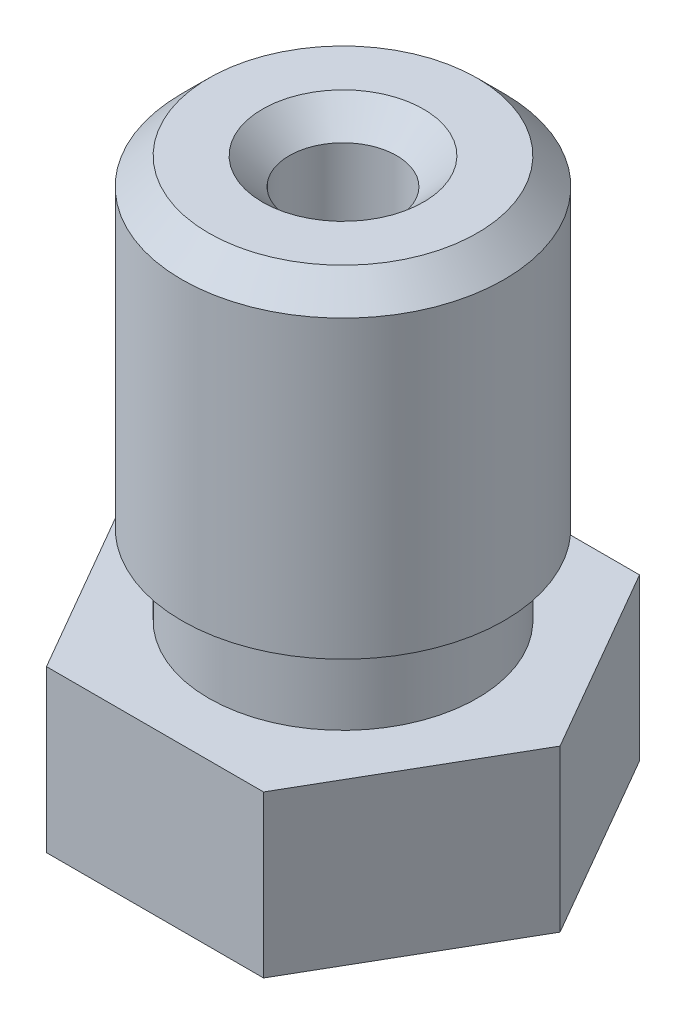
SolidWorks part; units mm, degrees
material "Brass"
ref_plane "Front Plane" through (0, 0, 0) normal (0, 0, 1) x (1, 0, 0)
ref_plane "Top Plane" through (0, 0, 0) normal (0, 1, 0) x (1, 0, 0)
ref_plane "Right Plane" through (0, 0, 0) normal (1, 0, 0) x (0, 0, -1)
ref_plane "Plane1" through (0, 0, 0) normal (0, -1, 0) x (1, 0, 0)
sketch "Sketch1" plane through (0, 0, 0) normal (0, -1, 0) x (1, 0, 0)
  line L0 (-2.0207, 3.5) -> (-4.0415, 0)
  line L1 (-4.0415, 0) -> (-2.0207, -3.5)
  line L2 (-2.0207, -3.5) -> (2.0207, -3.5)
  line L3 (2.0207, -3.5) -> (4.0415, 0)
  line L4 (4.0415, 0) -> (2.0207, 3.5)
  line L5 (2.0207, 3.5) -> (-2.0207, 3.5)
extrude "Boss-Extrude1" add sketch "Sketch1" against normal blind 3
ref_plane "Plane2" through (0, 0, 0) normal (0, 0, -1) x (-1, 0, 0)
sketch "Sketch2" plane through (0, 0, 0) normal (0, 0, -1) x (-1, 0, 0)
  line L0 (-2.5, 3) -> (0, 3)
  line L1 (0, 3) -> (0, 10.5)
  line L2 (0, 10.5) -> (-3, 10.5)
  line L3 (-3, 10.5) -> (-3, 4.5)
  line L4 (-3, 4.5) -> (-2.5, 4.5)
  line L5 (-2.5, 4.5) -> (-2.5, 3)
  line L6 (0, 3) -> (0, 10.5) construction
revolve "Revolve1" add sketch "Sketch2" angle 360 about L6
sketch "Sketch3" plane through (0, 0, 0) normal (0, 0, 1) x (1, 0, 0)
  line L0 (2.5, 0) -> (0, 0)
  line L1 (0, 0) -> (0, -2)
  line L2 (0, -2) -> (0.5, -2)
  line L3 (0.5, -2) -> (2.5, 0)
  line L4 (0, 0) -> (0, -2) construction
revolve "Revolve2" add sketch "Sketch3" angle 360 about L4
sketch "Sketch4" plane through (0, 0, 0) normal (0, 0, -1) x (-1, 0, 0)
  line L0 (-0.1, -2) -> (0, -2)
  line L1 (0, -2) -> (0, 10.5)
  line L2 (0, 10.5) -> (-1, 10.5)
  line L3 (-1, 10.5) -> (-1, 0)
  line L4 (-1, 0) -> (-0.75, -0.2273)
  line L5 (-0.75, -0.2273) -> (-0.75, -0.7)
  line L6 (-0.75, -0.7) -> (-0.1, -1.2)
  line L7 (-0.1, -1.2) -> (-0.1, -2)
  line L8 (0, -2) -> (0, 10.5) construction
  dimension "D1" = 1
  dimension "D2" = 0.1
  dimension "D3" = 0.75
  dimension "D4" = 0.5
  dimension "D5" = 0.8
  dimension "D6" = 0.2273
  dimension "D7" = 0.4727
revolve "Cut-Revolve1" cut sketch "Sketch4" angle 360 about L8
chamfer "Chamfer1" distance 0.5 angle 45 2 edges at (0, 10.5, 3) (0, 10.5, 1)
